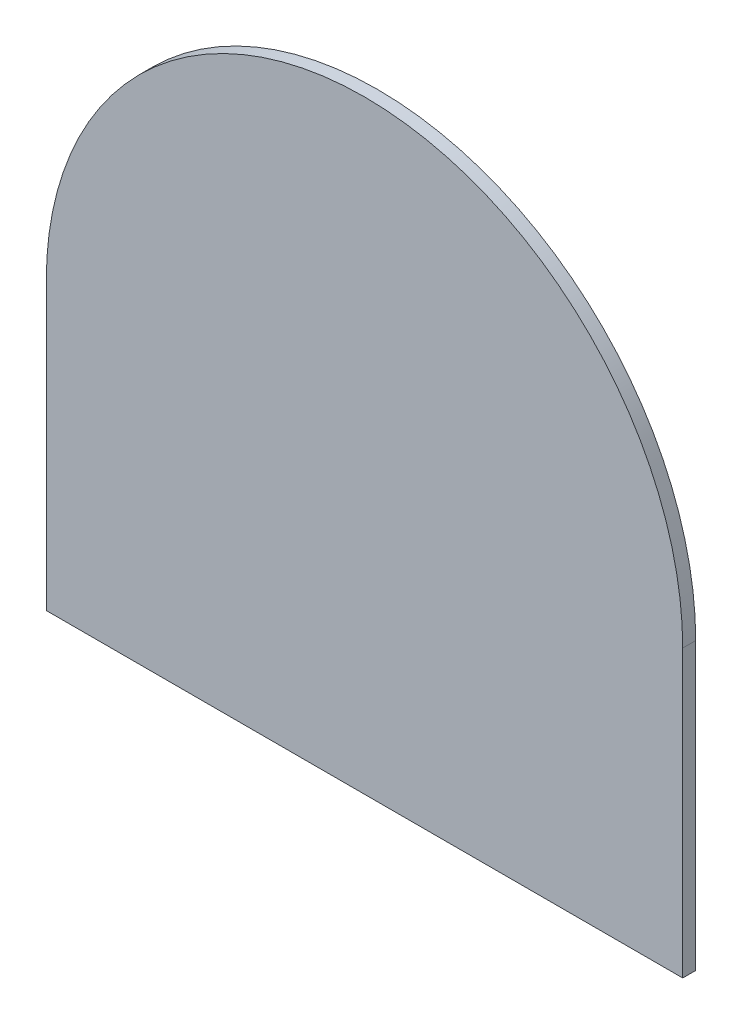
SolidWorks part; units mm, degrees
ref_plane "Plan de face" through (0, 0, 0) normal (0, 0, 1) x (1, 0, 0)
ref_plane "Plan de dessus" through (0, 0, 0) normal (0, 1, 0) x (1, 0, 0)
ref_plane "Plan de droite" through (0, 0, 0) normal (1, 0, 0) x (0, 0, -1)
sketch "Esquisse1" plane through (0, 0, 0) normal (0, 0, 1) x (1, 0, 0)
  line L1 (0, 0) -> (49, 0)
  line L2 (0, 0) -> (0, 22)
  line L4 (49, 0) -> (49, 22)
  arc A0 (24.5, 46.5) -> (49, 22) centre (24.5, 22) cw
  arc A1 (0, 22) -> (24.5, 46.5) centre (24.5, 22) cw
  point P9 (0, 0)
  dimension "D1" = 24.5
  dimension "D2" = 22
  dimension "D3" = 49
extrude "Boss.-Extru.1" add sketch "Esquisse1" along normal blind 1
